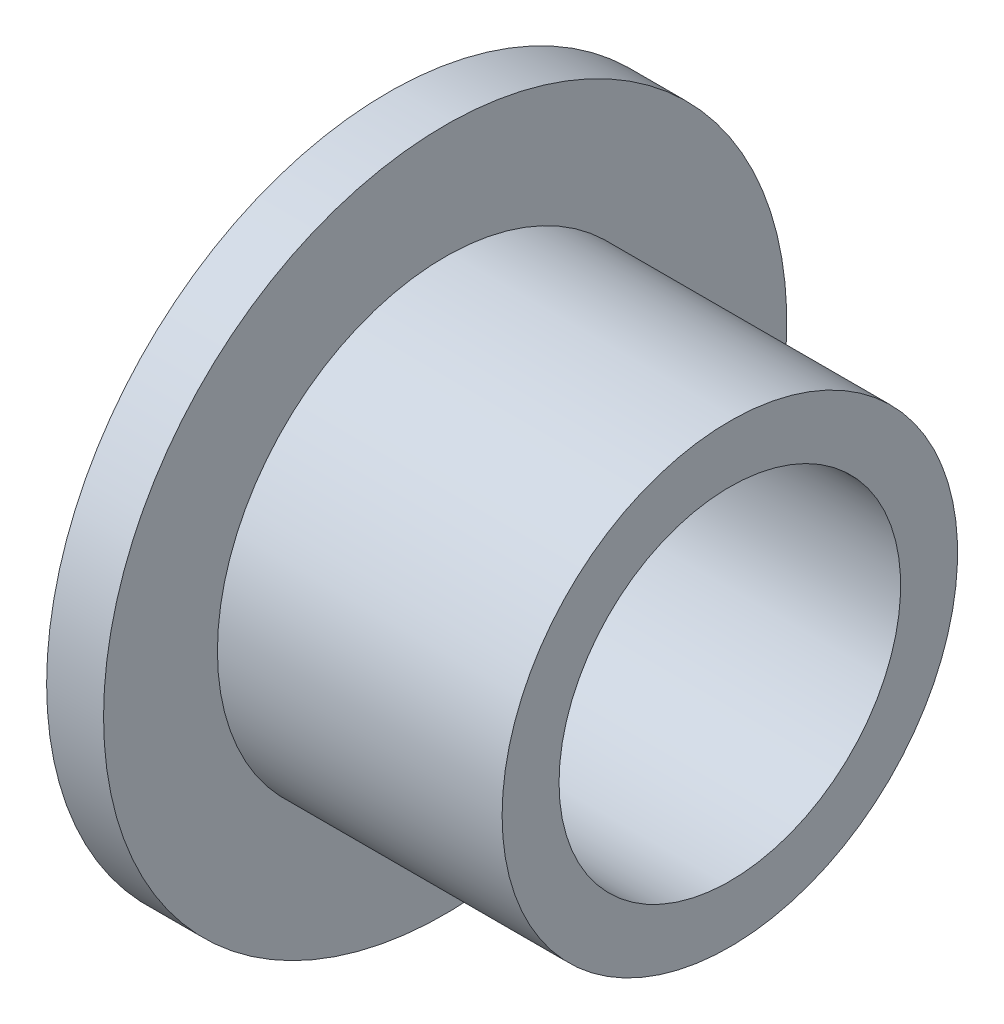
SolidWorks part; units mm, degrees
ref_plane "Vorne" through (0, 0, 0) normal (0, 0, 1) x (1, 0, 0)
ref_plane "Oben" through (0, 0, 0) normal (0, 1, 0) x (1, 0, 0)
ref_plane "Rechts" through (0, 0, 0) normal (1, 0, 0) x (0, 0, -1)
sketch "Skizze1" plane through (0, 0, 0) normal (0, 0, 1) x (1, 0, 0)
  line L0 (0, 0) -> (44.9745, 0) construction
  line L1 (0, 6) -> (0, 3)
  line L2 (0, 3) -> (6, 3)
  dimension "D1" = 6
  dimension "D2" = 6
  dimension "D3" = 12
revolve "Rotation-Dünn1" add sketch "Skizze1" angle 360 about L0 wall 1
move or copy body "Körper-Verschieben/Kopieren1" [suppressed] bodies to move or copy 103
